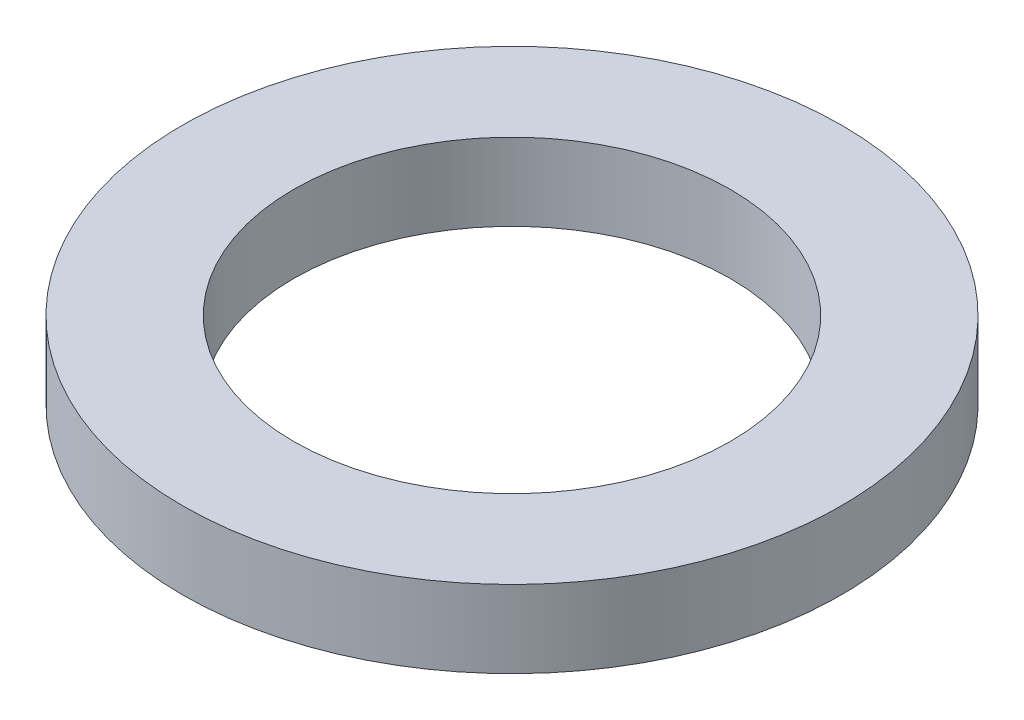
SolidWorks part; units mm, degrees
material "6061-T6 (SS)"
ref_plane "Front Plane" through (0, 0, 0) normal (0, 0, 1) x (1, 0, 0)
ref_plane "Top Plane" through (0, 0, 0) normal (0, 1, 0) x (1, 0, 0)
ref_plane "Right Plane" through (0, 0, 0) normal (1, 0, 0) x (0, 0, -1)
sketch "Sketch1" plane through (0, 0, 0) normal (0, 0, 1) x (1, 0, 0)
  line L0 (0, 22.7096) -> (0, -29.6046) construction
  line L2 (26.924, -9.525) -> (40.64, -9.525)
  line L3 (26.924, -9.525) -> (26.924, 0)
  line L4 (26.924, 0) -> (40.64, 0)
  line L5 (40.64, -9.525) -> (40.64, 0)
  dimension "D2" = 9.525
  dimension "D3" = 26.924
  dimension "D4" = 9.525
  dimension "D1" = 40.64
revolve "Revolve1" add sketch "Sketch1" angle 360 about L0
equation "\"D4@Sketch1\"=\"D2@Sketch1\""
